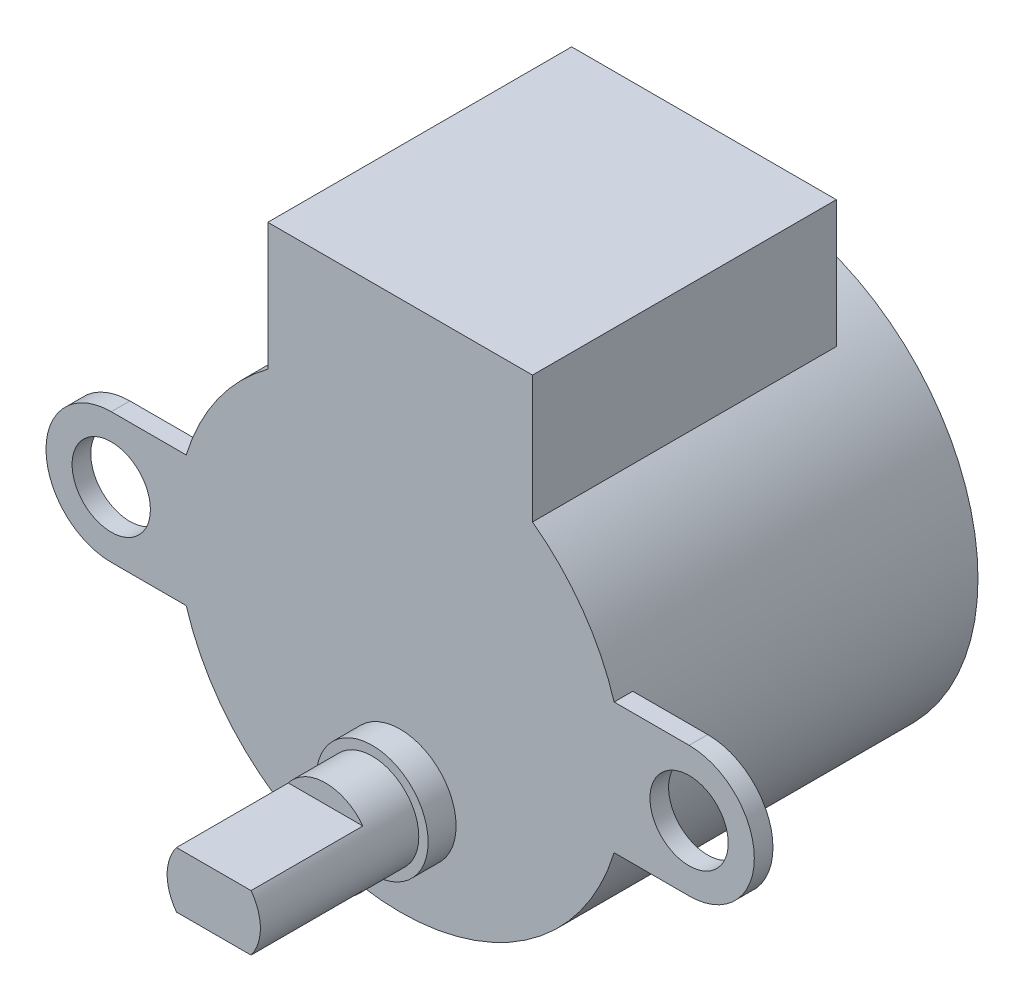
SolidWorks part; units mm, degrees
ref_plane "Front Plane" through (0, 0, 0) normal (0, 0, 1) x (1, 0, 0)
ref_plane "Top Plane" through (0, 0, 0) normal (0, 1, 0) x (1, 0, 0)
ref_plane "Right Plane" through (0, 0, 0) normal (1, 0, 0) x (0, 0, -1)
sketch "Sketch1" plane through (0, 0, 0) normal (0, 0, 1) x (1, 0, 0)
  line L0 (-7.1, 9.6742) -> (-7.1, 16.5)
  line L1 (-7.1, 16.5) -> (7.1, 16.5)
  line L2 (7.1, 16.5) -> (7.1, 9.6742)
  line L3 (0, 0) -> (0, 16.5) construction
  arc A0 (-7.1, 9.6742) -> (7.1, 9.6742) centre (0, 0) ccw
  dimension "D1" = 24
  dimension "D2" = 14.2
  dimension "D3" = 16.5
extrude "Boss-Extrude1" add sketch "Sketch1" along normal blind 19
sketch "Sketch2" plane through (0, 0, 0) normal (0, 0, -1) x (-1, 0, 0)
  line L0 (7.1, 16.5) -> (7.1, 9.6742) construction
  line L1 (-7.1, 16.5) -> (7.1, 16.5) construction
  line L2 (7.1, 16.5) -> (7.1, 9.6742)
  line L3 (-7.1, 16.5) -> (7.1, 16.5)
  line L4 (-7.1, 9.6742) -> (-7.1, 16.5) construction
  line L5 (-7.1, 9.6742) -> (-7.1, 16.5)
  arc A0 (-7.1, 9.6742) -> (7.1, 9.6742) centre (0, 0) ccw construction
  arc A1 (7.1, 9.6742) -> (-7.1, 9.6742) centre (0, 0) ccw
extrude "Cut-Extrude1" cut sketch "Sketch2" against normal blind 2.7
sketch "Sketch3" plane through (0, 0, 19) normal (0, 0, 1) x (1, 0, 0)
  line L0 (-15.5, 0) -> (15.5, 0) construction
  line L1 (-15.5, 3.5) -> (-11.4782, 3.5)
  line L2 (-15.5, -3.5) -> (-11.4782, -3.5)
  line L3 (11.4782, 3.5) -> (15.5, 3.5)
  line L4 (11.4782, -3.5) -> (15.5, -3.5)
  line L5 (0, 16.5) -> (0, 0) construction
  line L7 (7.1, 16.5) -> (-7.1, 16.5) construction
  arc A0 (-15.5, 3.5) -> (-15.5, -3.5) centre (-15.5, 0) ccw
  arc A1 (15.5, -3.5) -> (15.5, 3.5) centre (15.5, 0) ccw
  arc A2 (-7.1, 9.6742) -> (7.1, 9.6742) centre (0, 0) ccw construction
  arc A3 (-11.4782, 3.5) -> (-11.4782, -3.5) centre (0, 0) ccw
  arc A4 (11.4782, -3.5) -> (11.4782, 3.5) centre (0, 0) ccw
  circle A5 centre (-15.5, 0) radius 2.1
  circle A6 centre (15.5, 0) radius 2.1
  point P3 (0, 0)
  dimension "D2" = 3.5
  dimension "D3" = 4.2
  dimension "D1" = 31
extrude "Boss-Extrude2" add sketch "Sketch3" against normal blind 1
sketch "Sketch4" plane through (0, 0, 19) normal (0, 0, 1) x (1, 0, 0)
  line L0 (0, 0) -> (0, -6.5) construction
  circle A0 centre (0, -6.5) radius 3
  dimension "D1" = 6
  dimension "D2" = 6.5
extrude "Boss-Extrude3" add sketch "Sketch4" along normal blind 1.5
sketch "Sketch5" plane through (0, 0, 20.5) normal (0, 0, 1) x (1, 0, 0)
  circle A0 centre (0, -6.5) radius 2.5
  dimension "D2" = 5
extrude "Boss-Extrude5" add sketch "Sketch5" along direction (0, 0, -1) on the side of the normal blind 8.5
sketch "Sketch7" plane through (0, 0, 29) normal (0, 0, 1) x (1, 0, 0)
  line L0 (-2, -5) -> (2, -5)
  line L1 (-2, -8) -> (2, -8)
  arc A0 (2, -5) -> (-2, -5) centre (0, -6.5) ccw
  circle A1 centre (0, -6.5) radius 2.5
  arc A2 (-2, -8) -> (2, -8) centre (0, -6.5) ccw
  dimension "D2" = 3
  dimension "D1" = 0
extrude "Cut-Extrude2" cut sketch "Sketch7" against normal blind 6
